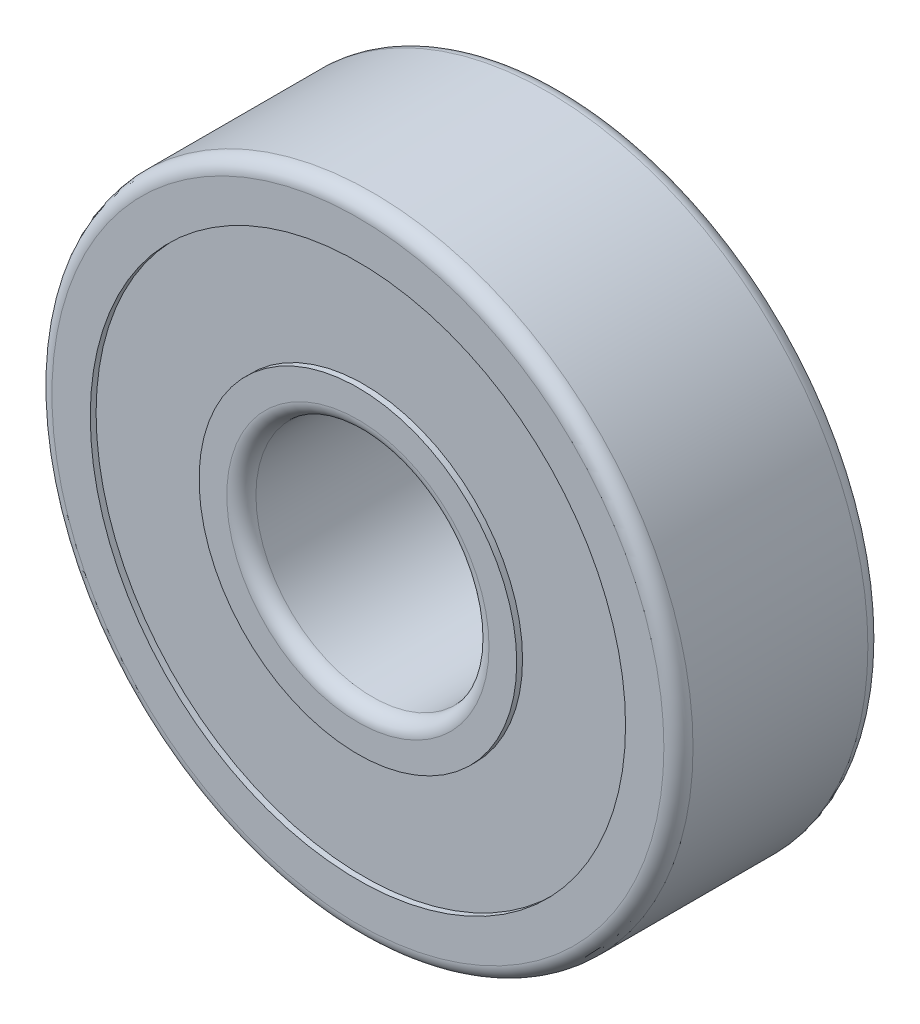
SolidWorks part; units mm, degrees
ref_plane "Płaszczyzna przednia" through (0, 0, 0) normal (0, 0, 1) x (1, 0, 0)
ref_plane "Płaszczyzna górna" through (0, 0, 0) normal (0, 1, 0) x (1, 0, 0)
ref_plane "Płaszczyzna prawa" through (0, 0, 0) normal (1, 0, 0) x (0, 0, -1)
sketch "Szkic1" plane through (0, 0, 0) normal (0, 0, 1) x (1, 0, 0)
  circle A0 centre (0, 0) radius 11
  circle A1 centre (0, 0) radius 4
  dimension "D1" = 8
  dimension "D2" = 22
extrude "Dodanie-wyciągnięcie1" add sketch "Szkic1" along normal mid plane 7
sketch "Szkic2" plane through (0, 0, 3.5) normal (0, 0, 1) x (1, 0, 0)
  circle A0 centre (0, 0) radius 5.4503
  circle A1 centre (0, 0) radius 9.1847
extrude "Wytnij-wyciągnięcie1" cut sketch "Szkic2" against normal blind 0.2
mirror "Lustro1" about plane through (0, 0, 0) normal (0, 0, 1) of "Wytnij-wyciągnięcie1"
fillet "Zaokrąglenie1" radius 0.5 4 edges at (4, 0, 3.5) (11, 0, 3.5) (11, 0, -3.5) (4, 0, -3.5)
